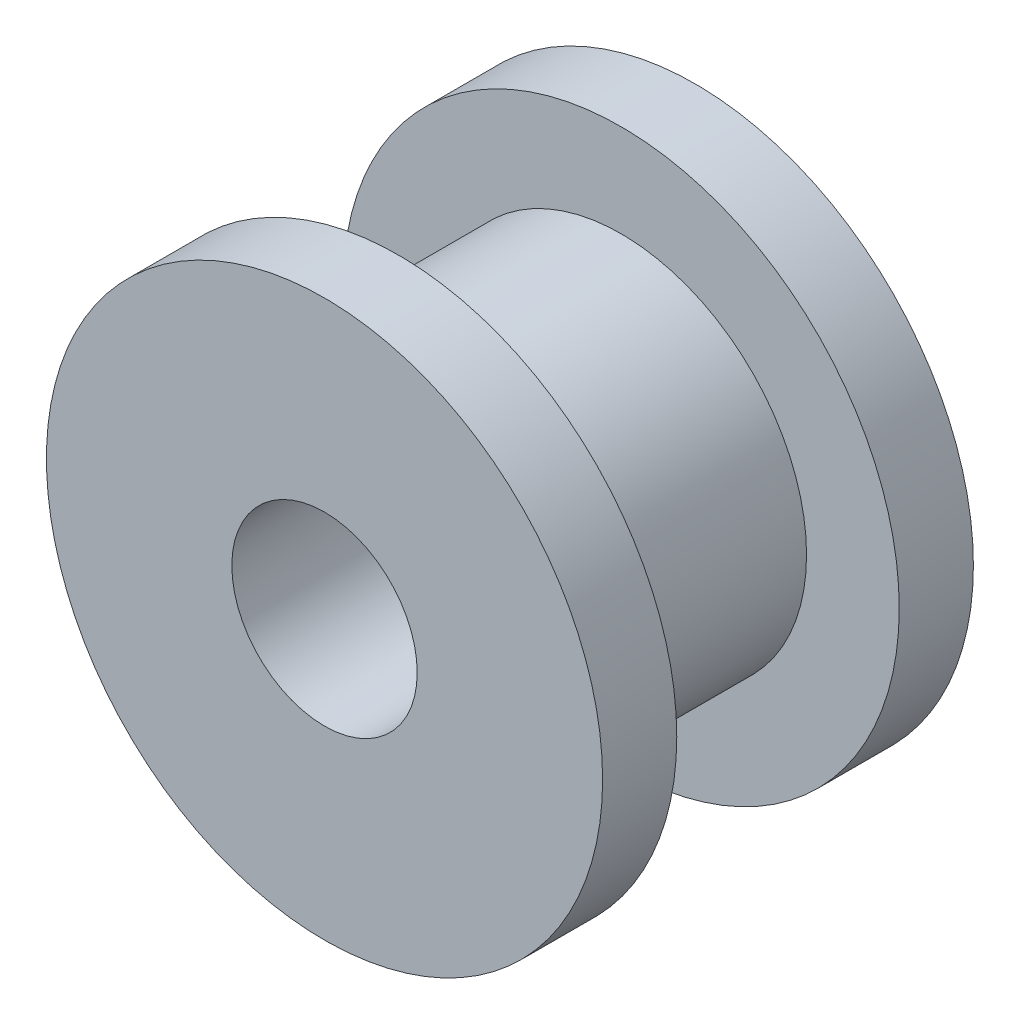
SolidWorks part; units mm, degrees
ref_plane "Front Plane" through (0, 0, 0) normal (0, 0, 1) x (1, 0, 0)
ref_plane "Top Plane" through (0, 0, 0) normal (0, 1, 0) x (1, 0, 0)
ref_plane "Right Plane" through (0, 0, 0) normal (1, 0, 0) x (0, 0, -1)
sketch "Sketch1" plane through (0, 0, 0) normal (0, 0, 1) x (1, 0, 0)
  circle A0 centre (0, 0) radius 9.525
  dimension "D1" = 19.05
extrude "Boss-Extrude1" add sketch "Sketch1" along normal blind 2.54
sketch "Sketch2" plane through (0, 0, 2.54) normal (0, 0, 1) x (1, 0, 0)
  circle A0 centre (0, 0) radius 6.35
  dimension "D1" = 12.7
extrude "Boss-Extrude2" add sketch "Sketch2" along normal blind 7.62
ref_plane "Plane1" through (0, 0, 6.35) normal (0, 0, 1) x (1, 0, 0)
mirror "Mirror1" about plane through (0, 0, 6.35) normal (0, 0, 1) of "Boss-Extrude1"
sketch "Sketch4" plane through (0, 0, 12.7) normal (0, 0, 1) x (1, 0, 0)
  circle A0 centre (0, 0) radius 3.175
  dimension "D1" = 6.35
extrude "Cut-Extrude1" cut sketch "Sketch4" against normal up to next
sketch "Sketch5" plane through (0, 0, 0) normal (0, 0, -1) x (-1, 0, 0)
  line L0 (0, 7.62) -> (0, -7.62) construction
  line L1 (-7.62, 0) -> (7.62, 0) construction
  circle A0 centre (0, 7.62) radius 1.5875
  circle A1 centre (7.62, 0) radius 1.5875
  circle A2 centre (0, -7.62) radius 1.5875
  circle A3 centre (-7.62, 0) radius 1.5875
  point P4 (0, 0)
  point P5 (0, 0)
  dimension "D2" = 3.175
  dimension "D1" = 7.62
